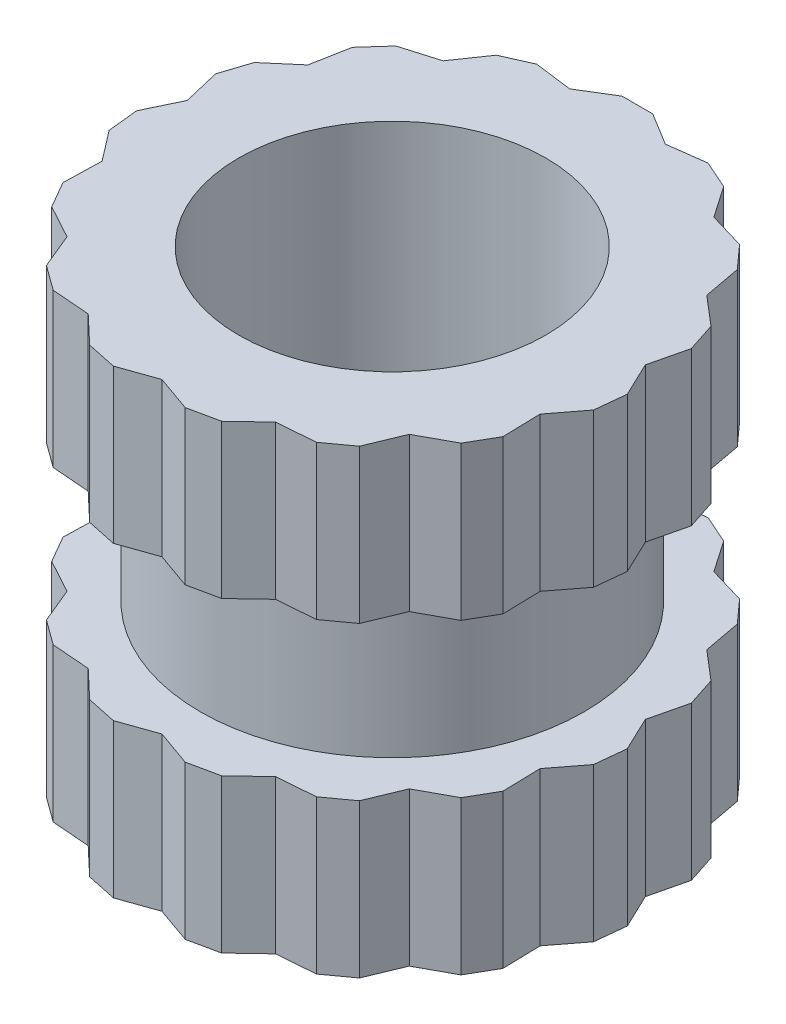
SolidWorks part; units mm, degrees
ref_plane "Front Plane" through (0, 0, 0) normal (0, 0, 1) x (1, 0, 0)
ref_plane "Top Plane" through (0, 0, 0) normal (0, 1, 0) x (1, 0, 0)
ref_plane "Right Plane" through (0, 0, 0) normal (1, 0, 0) x (0, 0, -1)
sketch "Sketch1" plane through (0, 0, 0) normal (0, 1, 0) x (1, 0, 0)
  circle A0 centre (0, 0) radius 1.25
  circle A1 centre (0, 0) radius 1
  dimension "D1" = 2.5
  dimension "D2" = 2
extrude "Boss-Extrude1" add sketch "Sketch1" along normal blind 1.5
sketch "Sketch2" plane through (0, 1.5, 0) normal (0, 1, 0) x (1, 0, 0)
  line L0 (0, 0) -> (0, 1.6) construction
  line L1 (0, 0) -> (-0.3327, 1.565) construction
  line L2 (-0.3119, 1.4672) -> (-0.1, 1.5969)
  line L3 (-0.1, 1.5969) -> (0.1, 1.5969)
  line L4 (0.3119, 1.4672) -> (0.5582, 1.4995)
  line L5 (0.3119, 1.4672) -> (0.1, 1.5969)
  line L6 (0.5582, 1.4995) -> (0.7409, 1.4181)
  line L7 (0.8817, 1.2135) -> (0.7409, 1.4181)
  line L8 (0.8817, 1.2135) -> (1.1198, 1.1428)
  line L9 (1.1198, 1.1428) -> (1.2536, 0.9942)
  line L10 (1.299, 0.75) -> (1.2536, 0.9942)
  line L11 (1.299, 0.75) -> (1.4878, 0.5886)
  line L12 (1.4878, 0.5886) -> (1.5496, 0.3984)
  line L13 (1.4918, 0.1568) -> (1.5496, 0.3984)
  line L14 (1.4918, 0.1568) -> (1.5986, -0.0675)
  line L15 (1.5986, -0.0675) -> (1.5777, -0.2664)
  line L16 (1.4266, -0.4635) -> (1.5777, -0.2664)
  line L17 (1.4266, -0.4635) -> (1.4329, -0.7118)
  line L18 (1.4329, -0.7118) -> (1.3329, -0.885)
  line L19 (1.1147, -1.0037) -> (1.3329, -0.885)
  line L20 (1.1147, -1.0037) -> (1.0195, -1.2331)
  line L21 (1.0195, -1.2331) -> (0.8577, -1.3507)
  line L22 (0.6101, -1.3703) -> (0.8577, -1.3507)
  line L23 (0.6101, -1.3703) -> (0.4298, -1.5412)
  line L24 (0.4298, -1.5412) -> (0.2342, -1.5828)
  line L25 (0, -1.5) -> (0.2342, -1.5828)
  line L26 (0, -1.5) -> (-0.2342, -1.5828)
  line L27 (-0.2342, -1.5828) -> (-0.4298, -1.5412)
  line L28 (-0.6101, -1.3703) -> (-0.4298, -1.5412)
  line L29 (-0.6101, -1.3703) -> (-0.8577, -1.3507)
  line L30 (-0.8577, -1.3507) -> (-1.0195, -1.2331)
  line L31 (-1.1147, -1.0037) -> (-1.0195, -1.2331)
  line L32 (-1.1147, -1.0037) -> (-1.3329, -0.885)
  line L33 (-1.3329, -0.885) -> (-1.4329, -0.7118)
  line L34 (-1.4266, -0.4635) -> (-1.4329, -0.7118)
  line L35 (-1.4266, -0.4635) -> (-1.5777, -0.2664)
  line L36 (-1.5777, -0.2664) -> (-1.5986, -0.0675)
  line L37 (-1.4918, 0.1568) -> (-1.5986, -0.0675)
  line L38 (-1.4918, 0.1568) -> (-1.5496, 0.3984)
  line L39 (-1.5496, 0.3984) -> (-1.4878, 0.5886)
  line L40 (-1.299, 0.75) -> (-1.4878, 0.5886)
  line L41 (-1.299, 0.75) -> (-1.2536, 0.9942)
  line L42 (-1.2536, 0.9942) -> (-1.1198, 1.1428)
  line L43 (-0.8817, 1.2135) -> (-1.1198, 1.1428)
  line L44 (-0.8817, 1.2135) -> (-0.7409, 1.4181)
  line L45 (-0.7409, 1.4181) -> (-0.5582, 1.4995)
  line L46 (-0.3119, 1.4672) -> (-0.5582, 1.4995)
  circle A22 centre (0, 0) radius 1 construction
  circle A23 centre (0, 0) radius 1
  circle A24 centre (0, 0) radius 1.6
  circle A25 centre (0, 0) radius 1.5
  point P69 (0, 0)
  dimension "D1" = 3.2
  dimension "D2" = 3
  dimension "D3" = 12
  dimension "D4" = 0.2
extrude "Boss-Extrude2" add sketch "Sketch2" against normal blind 1
mirror "Mirror1" about plane through (0, 0, 0) normal (0, 1, 0) of "Boss-Extrude1", "Boss-Extrude2"
